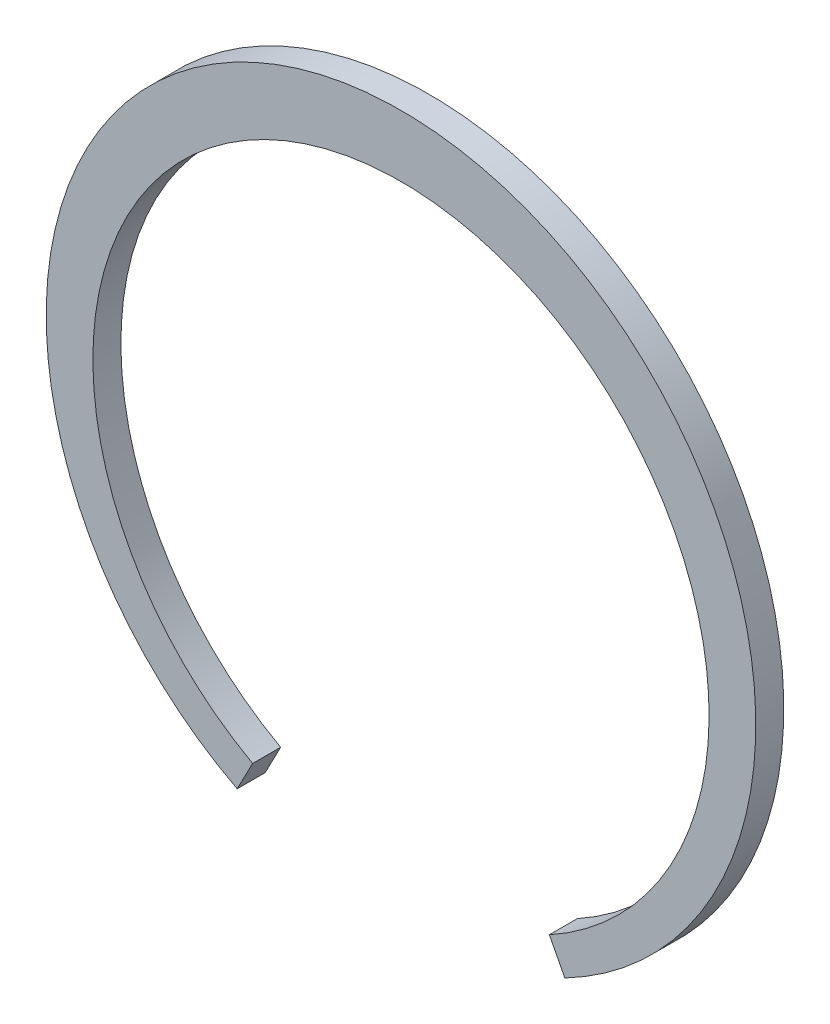
SolidWorks part; units mm, degrees
ref_plane "Ebene vorne" through (0, 0, 0) normal (0, 0, 1) x (1, 0, 0)
ref_plane "Ebene oben" through (0, 0, 0) normal (0, 1, 0) x (1, 0, 0)
ref_plane "Ebene rechts" through (0, 0, 0) normal (1, 0, 0) x (0, 0, -1)
sketch "Skizze1" plane through (0, 0, 0) normal (0, 0, 1) x (1, 0, 0)
  line L0 (0, 0) -> (0, -33.387) construction
  line L1 (-7.9446, -15.2614) -> (-8.7732, -16.8532)
  line L2 (7.9446, -15.2614) -> (8.7732, -16.8532)
  arc A0 (8.7732, -16.8532) -> (-8.7732, -16.8532) centre (0, 0) ccw
  arc A1 (7.9446, -15.2614) -> (-7.9446, -15.2614) centre (0, -0.8) ccw
  dimension "D1" = 38
  dimension "D2" = 33
  dimension "D3" = 0.8
  dimension "D4" = 55
extrude "Aufsatz-Linear austragen1" add sketch "Skizze1" along normal blind 1.5
sketch "Skizze5" plane through (0, 0, 1.5) normal (0, 0, 1) x (1, 0, 0)
  arc A0 (7.9446, -15.2614) -> (-7.9446, -15.2614) centre (0, -0.8) ccw construction
  arc A1 (7.9446, -15.2614) -> (-7.9446, -15.2614) centre (0, -0.8) ccw
  arc A2 (-7.9446, -15.2614) -> (-13.201, -10.6987) centre (-10.8161, -13.2604) ccw
  point P5 (0, 0)
  dimension "D1" = 7
